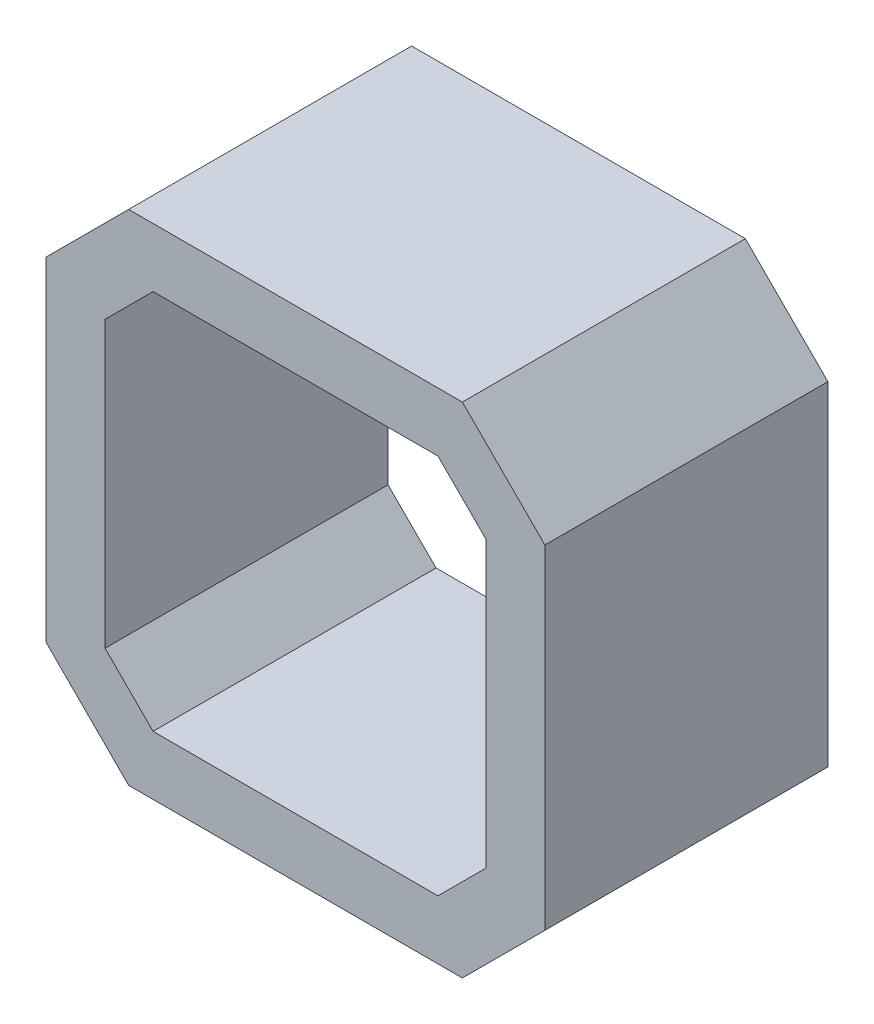
SolidWorks part; units mm, degrees
ref_plane "Front Plane" through (0, 0, 0) normal (0, 0, 1) x (1, 0, 0)
ref_plane "Top Plane" through (0, 0, 0) normal (0, 1, 0) x (1, 0, 0)
ref_plane "Right Plane" through (0, 0, 0) normal (1, 0, 0) x (0, 0, -1)
sketch "Sketch1" plane through (0, 0, 0) normal (0, 0, 1) x (1, 0, 0)
  line L0 (-21.15, 14.15) -> (-14.15, 21.15)
  line L1 (-14.15, 21.15) -> (14.15, 21.15)
  line L2 (-21.15, 14.15) -> (-21.15, -14.15)
  line L3 (-14.15, -21.15) -> (14.15, -21.15)
  line L4 (21.15, 14.15) -> (21.15, -14.15)
  line L5 (-21.15, 21.15) -> (21.15, -21.15) construction
  line L6 (-21.15, -21.15) -> (21.15, 21.15) construction
  line L7 (14.15, 21.15) -> (21.15, 14.15)
  line L8 (14.15, -21.15) -> (21.15, -14.15)
  line L9 (-21.15, -14.15) -> (-14.15, -21.15)
  line L10 (-16.15, 12.0789) -> (-12.0789, 16.15)
  line L11 (-12.0789, 16.15) -> (12.0789, 16.15)
  line L12 (12.0789, 16.15) -> (16.15, 12.0789)
  line L13 (16.15, 12.0789) -> (16.15, -12.0789)
  line L14 (12.0789, -16.15) -> (16.15, -12.0789)
  line L15 (-12.0789, -16.15) -> (12.0789, -16.15)
  line L16 (-16.15, -12.0789) -> (-12.0789, -16.15)
  line L17 (-16.15, 12.0789) -> (-16.15, -12.0789)
  point P0 (0, 0)
  dimension "D1" = 42.3
  dimension "D2" = 42.3
  dimension "D3" = 5
extrude "Boss-Extrude1" add sketch "Sketch1" along normal mid plane 24
